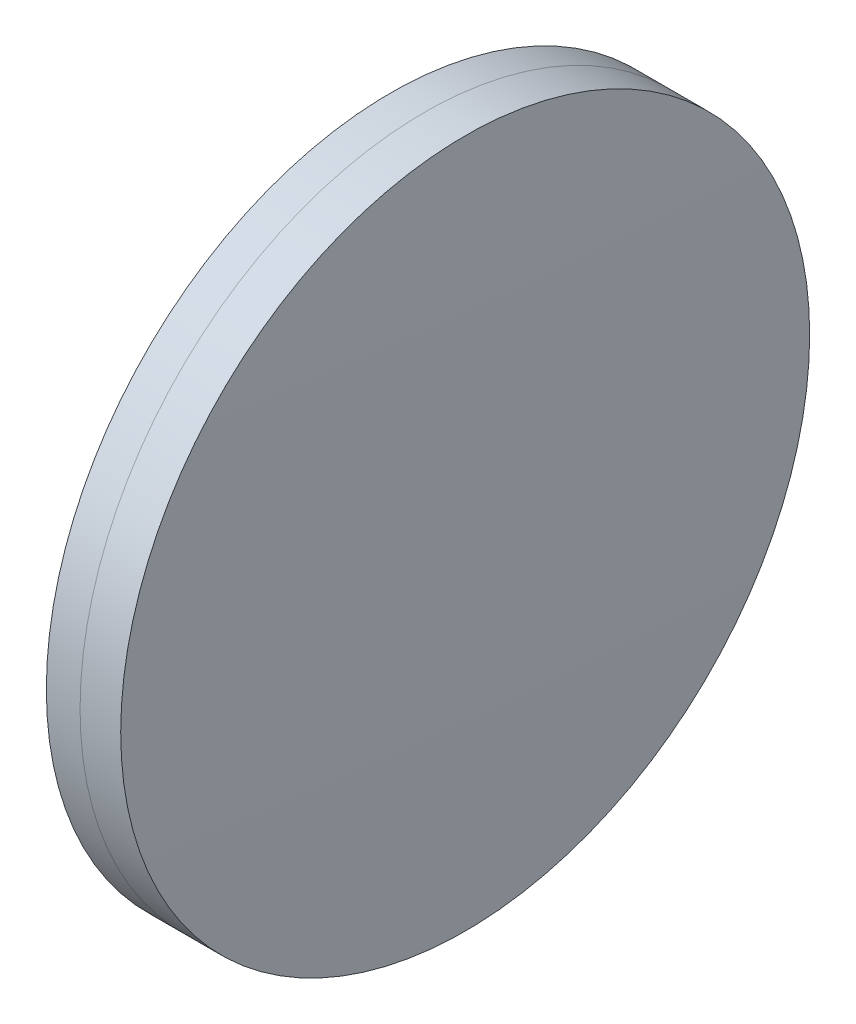
SolidWorks part; units mm, degrees
ref_plane "前视基准面" through (0, 0, 0) normal (0, 0, 1) x (1, 0, 0)
ref_plane "上视基准面" through (0, 0, 0) normal (0, 1, 0) x (1, 0, 0)
ref_plane "右视基准面" through (0, 0, 0) normal (1, 0, 0) x (0, 0, -1)
sketch "草图1" plane through (0, 0, 0) normal (0, 1, 0) x (1, 0, 0)
  line L0 (124.5233, 0) -> (546.9115, 0) construction
  line L1 (497.1064, -25.4) -> (499.5923, -25.4)
  line L2 (497.1064, 25.4) -> (499.5923, 25.4)
  arc A0 (499.5923, -25.4) -> (499.5923, 25.4) centre (257.6218, 0) ccw
  arc A1 (497.1064, 25.4) -> (497.1064, -25.4) centre (768.8218, 0) ccw
  point P4 (546.9115, 0)
  point P10 (495.9218, 0)
  point P11 (500.9218, 0)
  dimension "D3" = 272.9
  dimension "D4" = 243.3
  dimension "D1" = 25.4
  dimension "D2" = 25.4
  dimension "D5" = 5
revolve "旋转1" add sketch "草图1" angle 360 about L0
sketch "草图2" plane through (0, 0, 0) normal (0, 1, 0) x (1, 0, 0)
  line L0 (-0.5519, 0) -> (546.7349, 0) construction
  line L2 (499.5923, 25.4) -> (502.5892, 25.4)
  line L3 (499.5923, -25.4) -> (502.5892, -25.4)
  arc A0 (502.5892, -25.4) -> (502.5892, 25.4) centre (-467.0782, 0) ccw
  arc A1 (499.5923, -25.4) -> (499.5923, 25.4) centre (257.6218, 0) ccw construction
  arc A2 (499.5923, -25.4) -> (499.5923, 25.4) centre (257.6218, 0) ccw
  point P4 (500.9218, 0)
  point P8 (502.9218, 0)
  point P9 (546.7349, 0)
  dimension "D1" = 970
  dimension "D2" = 2
revolve "旋转3" add sketch "草图2" angle 360 about L0
